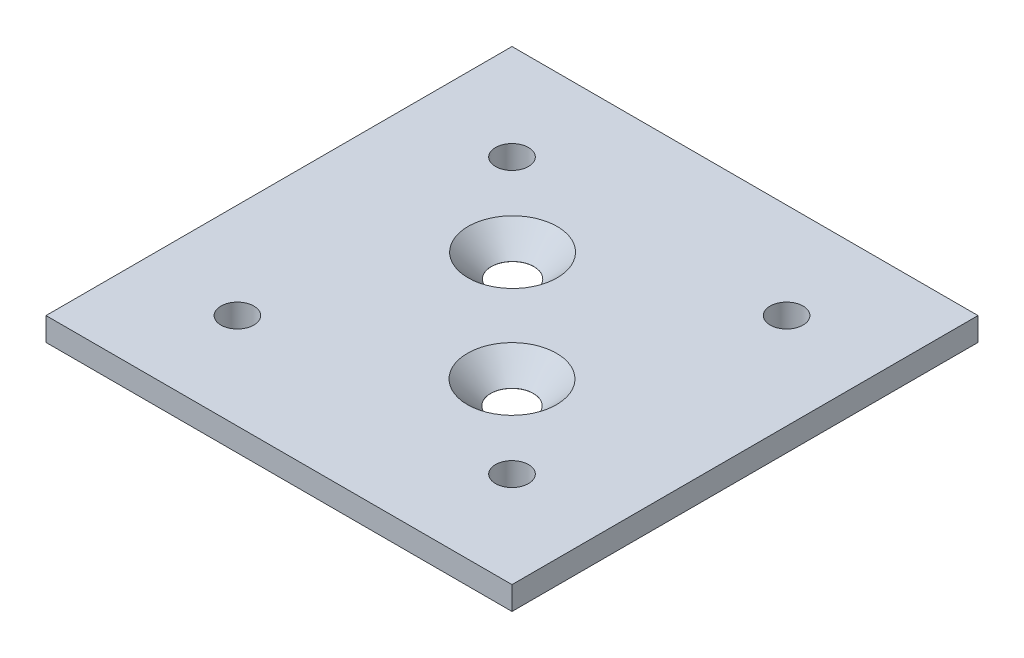
SolidWorks part; units mm, degrees
ref_plane "Alzado" through (0, 0, 0) normal (0, 0, 1) x (1, 0, 0)
ref_plane "Planta" through (0, 0, 0) normal (0, 1, 0) x (1, 0, 0)
ref_plane "Vista lateral" through (0, 0, 0) normal (1, 0, 0) x (0, 0, -1)
sketch "Croquis1" plane through (0, 0, 0) normal (0, 1, 0) x (1, 0, 0)
  line L0 (0, 60) -> (60, 0) construction
  line L1 (0, 0) -> (60, 0)
  line L2 (0, 0) -> (0, 60)
  line L3 (0, 60) -> (60, 60)
  line L4 (60, 0) -> (60, 60)
  line L5 (0, 0) -> (60, 60) construction
  line L6 (30, 60) -> (30, 0) construction
  line L7 (0, 30) -> (60, 30) construction
  circle A0 centre (30, 30) radius 25 construction
  circle A1 centre (12.3223, 47.6777) radius 2.125
  circle A2 centre (12.3223, 12.3223) radius 2.125
  circle A3 centre (47.6777, 12.3223) radius 2.125
  circle A4 centre (47.6777, 47.6777) radius 2.125
  circle A5 centre (22.9664, 37.1083) radius 0.5
  circle A6 centre (37.0711, 22.9289) radius 0.5
  circle A7 centre (30, 30) radius 10 construction
  dimension "D3" = 50
  dimension "D4" = 4.25
  dimension "D6" = 1
  dimension "D8" = 20
  dimension "D1" = 60
  dimension "D2" = 60
  dimension "D5" = 4
extrude "Saliente-Extruir1" add sketch "Croquis1" along normal blind 3
hole_wizard "Avellanado para tornillo con cabeza avellanada de clavija hexagonal de M53" positions "Croquis9" profile "Croquis8" countersink size "M5" standard "DIN" end condition through all
sketch "Croquis9" plane through (0, 3, 0) normal (0, 1, 0) x (1, 0, 0)
  point P0 (22.9664, 37.1083)
  point P3 (37.0711, 22.9289)
sketch "Croquis8" plane through (22.9664, 3, -37.1083) normal (1, 0, 0) x (0, 0, 1)
  line L0 (0, 0) -> (0, 3)
  line L1 (0, 3) -> (2.75, 3)
  line L2 (2.75, 3) -> (2.75, 2.985)
  line L3 (2.75, 2.985) -> (5.735, 0)
  line L5 (5.735, 0) -> (0, 0)
  line L6 (-2.75, 2.985) -> (-5.735, 0) construction
  line L11 (0, -6.35) -> (0, 107.95) construction
  dimension "Diámetro de taladro hasta el siguiente" = 5.5
  dimension "Profundidad de taladro hasta el siguiente" = 3
  dimension "Diámetro de avellanado cercano" = 11.47
  dimension "Ángulo de avellanado cercano" = 90
